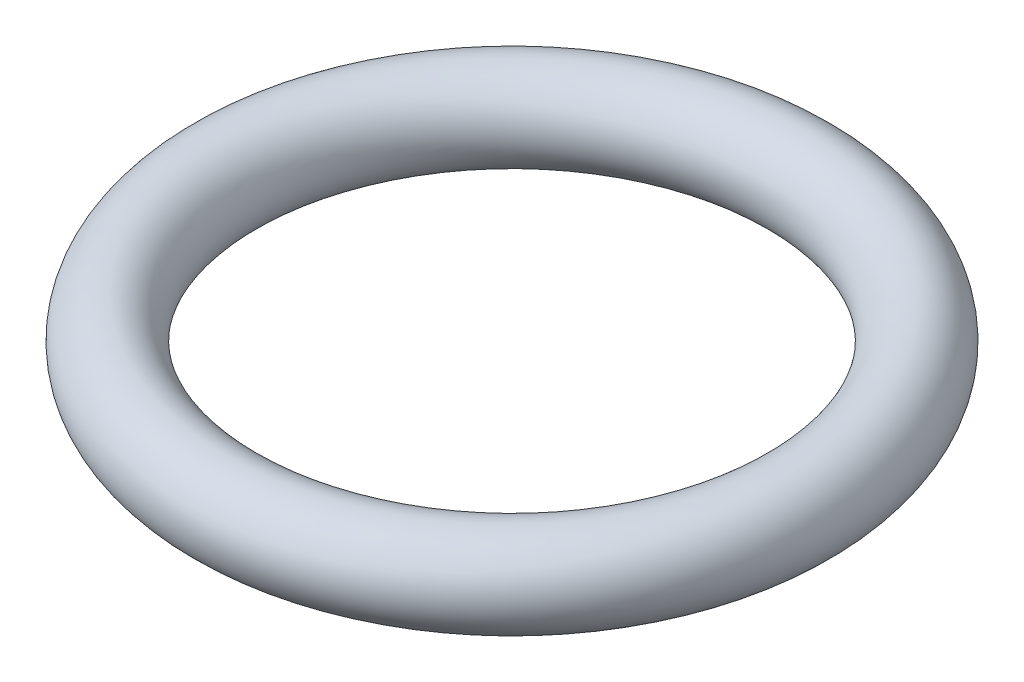
SolidWorks part; units mm, degrees
ref_plane "Alzado" through (0, 0, 0) normal (0, 0, 1) x (1, 0, 0)
ref_plane "Planta" through (0, 0, 0) normal (0, 1, 0) x (1, 0, 0)
ref_plane "Vista lateral" through (0, 0, 0) normal (1, 0, 0) x (0, 0, -1)
sketch "Croquis1" plane through (0, 0, 0) normal (0, 0, 1) x (1, 0, 0)
  line L0 (0, 7.9327) -> (0, -9.0865) construction
  circle A0 centre (8.25, 0) radius 1.25
  dimension "D1" = 2.5
  dimension "D2" = 8.25
revolve "Revolución1" add sketch "Croquis1" angle 360 about L0
